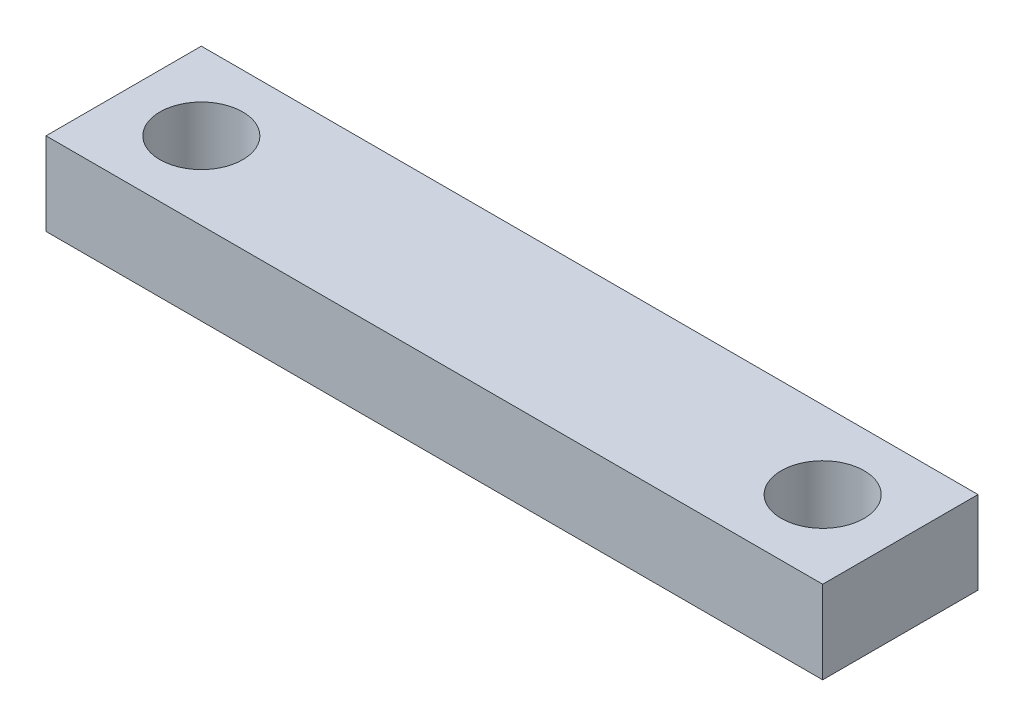
SolidWorks part; units mm, degrees
ref_plane "Front Plane" through (0, 0, 0) normal (0, 0, 1) x (1, 0, 0)
ref_plane "Top Plane" through (0, 0, 0) normal (0, 1, 0) x (1, 0, 0)
ref_plane "Right Plane" through (0, 0, 0) normal (1, 0, 0) x (0, 0, -1)
sketch "Sketch2" plane through (0, 0, 0) normal (0, 1, 0) x (1, 0, 0)
  line L0 (-37.5, 0) -> (37.5, 0)
  line L1 (-37.5, 7.5) -> (37.5, 7.5)
  line L2 (-37.5, 7.5) -> (-37.5, -7.5)
  line L3 (-37.5, -7.5) -> (37.5, -7.5)
  line L4 (37.5, 7.5) -> (37.5, -7.5)
  line L5 (-37.5, 7.5) -> (37.5, -7.5) construction
  line L6 (-37.5, -7.5) -> (37.5, 7.5) construction
  circle A0 centre (-30, 0) radius 4
  circle A1 centre (30, 0) radius 4
  point P0 (0, 0)
  dimension "D3" = 8
  dimension "D4" = 8
  dimension "D1" = 75
  dimension "D2" = 15
  dimension "D5" = 7.5
  dimension "D6" = 7.5
extrude "Boss-Extrude1" add sketch "Sketch2" along normal blind 8 contours A1 L0 L4 L1 L2 A0 | A1 L0 A0 L2 L3 L4
